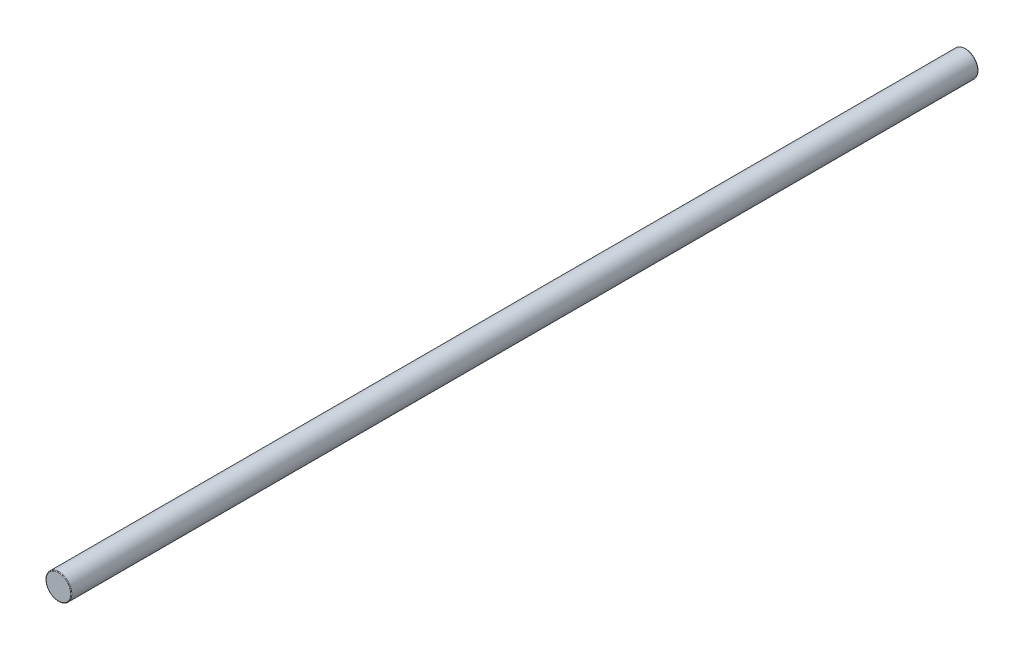
SolidWorks part; units mm, degrees
material "Acero al carbono no aleado"
ref_plane "Front Plane" through (0, 0, 0) normal (0, 0, 1) x (1, 0, 0)
ref_plane "Top Plane" through (0, 0, 0) normal (0, 1, 0) x (1, 0, 0)
ref_plane "Right Plane" through (0, 0, 0) normal (1, 0, 0) x (0, 0, -1)
sketch "Sketch1" plane through (0, 0, 0) normal (0, 0, 1) x (1, 0, 0)
  circle A0 centre (0, 0) radius 4
  dimension "D1" = 8
extrude "Boss-Extrude1" add sketch "Sketch1" against normal blind 283
fillet "Fillet1" radius 0.2 2 edges at (4, 0, -283) (4, 0, 0)
sketch "Sketch2" plane through (0, 0, 0) normal (0, 0, 1) x (1, 0, 0)
  circle A0 centre (0, 0) radius 4
  dimension "D1" = 8
sketch "Sketch3" plane through (0, 0, 0) normal (0, 1, 0) x (1, 0, 0)
  line L0 (3, 0.35) -> (3, 0.05)
  line L1 (3, 0.05) -> (5, -0.75)
  line L2 (5, -0.75) -> (5, 1.15)
  line L3 (5, 1.15) -> (3, 0.35)
  line L4 (5, 0.2) -> (3, 0.2)
  line L7 (4, 0.2) -> (-4, 0.2) construction
  point P7 (4, 0.2)
  dimension "D1" = 1.9
  dimension "D2" = 2
  dimension "D3" = 0.3
  dimension "D4" = 4
curve "Helix/Spiral1" pitch 2 height 300 turns 150
